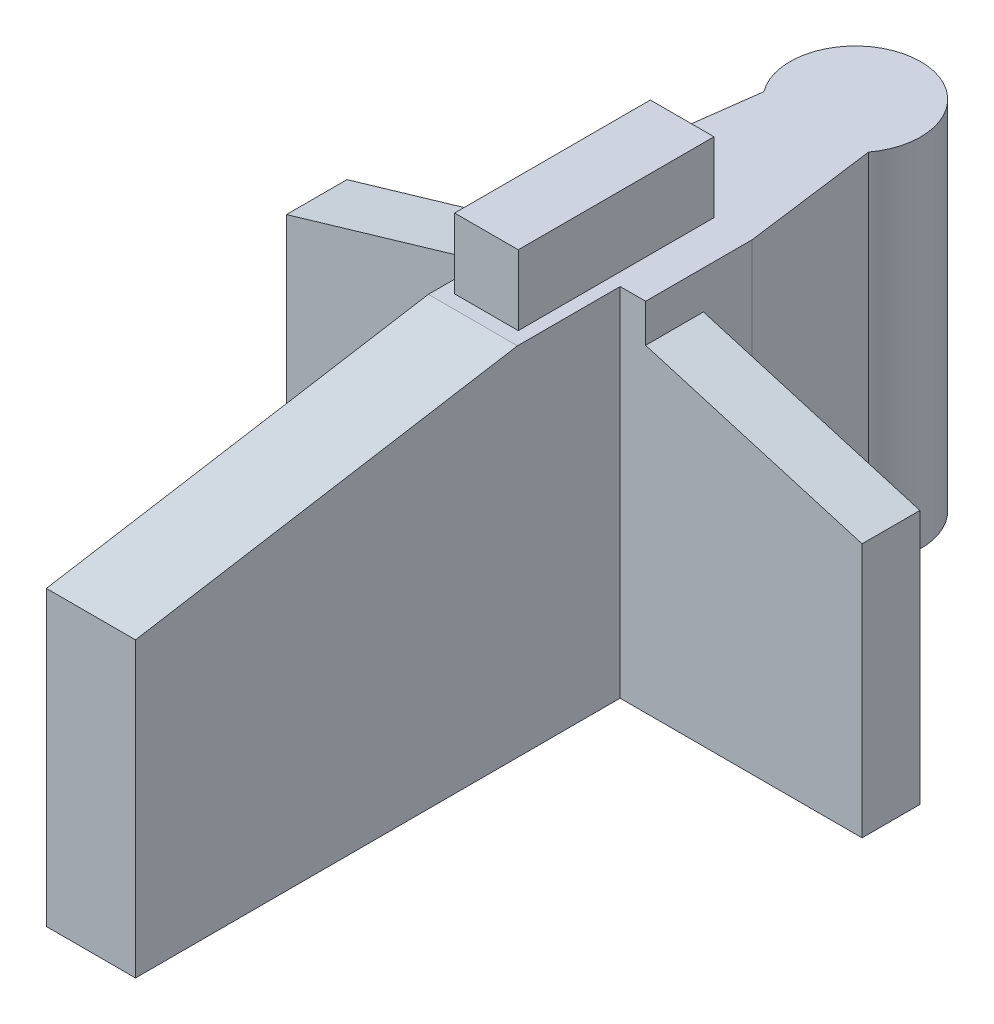
SolidWorks part; units mm, degrees
ref_plane "Front Plane" through (0, 0, 0) normal (0, 0, 1) x (1, 0, 0)
ref_plane "Top Plane" through (0, 0, 0) normal (0, 1, 0) x (1, 0, 0)
ref_plane "Right Plane" through (0, 0, 0) normal (1, 0, 0) x (0, 0, -1)
sketch "Sketch2" plane through (0, 0, 0) normal (0, 1, 0) x (1, 0, 0)
  line L0 (-162.9677, 548.3217) -> (265.9034, 766.8425) construction
  line L1 (-248.772, 683.8905) -> (-250.1636, 673.3634)
  line L2 (-241.1636, 664.9903) -> (-222.1636, 664.9903)
  line L4 (-267.1636, 669.5334) -> (-250.1636, 669.5334)
  line L5 (-267.1636, 669.5334) -> (-267.1636, 664.7834)
  line L6 (-267.1636, 664.7834) -> (-248.1636, 664.7834)
  line L7 (-222.1636, 669.5334) -> (-222.1636, 664.9903)
  line L9 (-250.1636, 669.5334) -> (-250.1636, 673.3634)
  line L10 (-240.5552, 683.8905) -> (-239.1636, 673.3624)
  line L11 (-239.1636, 669.5334) -> (-239.1636, 673.3624)
  line L13 (-239.1636, 669.5334) -> (-222.1636, 669.5334)
  line L16 (-244.6636, 626.9286) -> (-241.1636, 626.9286)
  line L17 (-241.1636, 664.9903) -> (-241.1636, 626.9286)
  line L18 (-244.6636, 626.9286) -> (-248.1636, 626.9286)
  line L21 (-248.1636, 626.9286) -> (-248.1636, 664.7834)
  arc A0 (-240.5552, 683.8905) -> (-248.772, 683.8905) centre (-244.6636, 686.9632) ccw
  dimension "D8" = 19
  dimension "D1" = 4.75
  dimension "D2" = 3.829
  dimension "D3" = 3.83
  dimension "D4" = 45
  dimension "D6" = 17
  dimension "D7" = 19
  dimension "D9" = 7
  dimension "D10" = 17
  dimension "D11" = 11
extrude "Boss-Extrude1" add sketch "Sketch2" along normal blind 28
sketch "Sketch6" plane through (0, 28, 0) normal (0, 1, 0) x (1, 0, 0)
  line L0 (-250.1636, 673.3634) -> (-239.1636, 673.3624) construction
  line L1 (-241.1636, 664.9903) -> (-222.1636, 664.9903) construction
  line L2 (-244.6636, 673.3629) -> (-242.1636, 673.3629)
  line L4 (-244.6636, 657.9903) -> (-242.1636, 657.9903)
  line L5 (-242.1636, 673.3629) -> (-242.1636, 657.9903)
  line L6 (-244.6636, 657.9903) -> (-247.1636, 657.9903)
  line L7 (-244.6636, 673.3629) -> (-244.6636, 673.3631)
  line L8 (-244.6636, 673.3631) -> (-247.1636, 673.3631)
  line L9 (-247.1636, 657.9903) -> (-247.1636, 673.3631)
  dimension "D1" = 7
  dimension "D2" = 2.5
  dimension "D3" = 2.5
extrude "Boss-Extrude2" add sketch "Sketch6" along normal blind 5.5
sketch "Sketch8" plane through (0, 0, -669.5334) normal (0, 0, -1) x (-1, 0, 0)
  line L0 (267.1636, 20) -> (250.1636, 25)
  line L1 (222.1636, 28) -> (222.1636, 0) construction
  line L2 (250.1636, 28) -> (250.1636, 0) construction
  line L3 (267.1636, 28) -> (267.1636, 0) construction
  line L4 (250.1636, 28) -> (267.1636, 28)
  line L5 (267.1636, 28) -> (267.1636, 20)
  line L6 (222.1636, 20) -> (222.1636, 28)
  line L7 (222.1636, 28) -> (239.1636, 28)
  line L8 (250.1636, 25) -> (250.1636, 28)
  line L9 (222.1636, 20) -> (239.1636, 25)
  line L10 (239.1636, 28) -> (239.1636, 0) construction
  line L11 (239.1636, 25) -> (239.1636, 28)
  dimension "D1" = 8
  dimension "D2" = 8
  dimension "D3" = 3
  dimension "D4" = 3
extrude "Cut-Extrude1" cut sketch "Sketch8" against normal blind 5.5
sketch "Sketch9" plane through (-248.1636, 0, 0) normal (-1, 0, 0) x (0, 0, 1)
  line L0 (-626.9286, 28) -> (-626.9286, 23)
  line L1 (-626.9286, 28) -> (-626.9286, 0) construction
  line L2 (-626.9286, 23) -> (-656.9286, 28)
  line L3 (-664.7834, 28) -> (-626.9286, 28) construction
  line L4 (-656.9286, 28) -> (-626.9286, 28)
  dimension "D1" = 30
  dimension "D2" = 5
extrude "Cut-Extrude2" cut sketch "Sketch9" against normal blind 8
